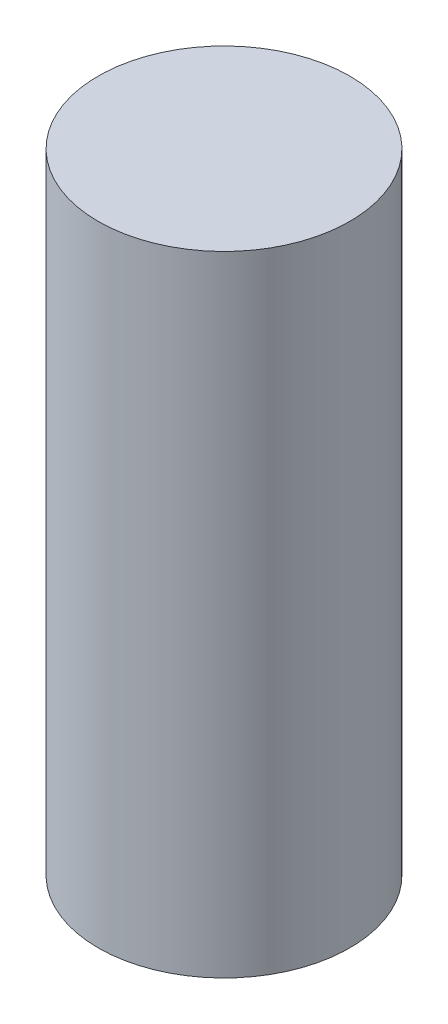
SolidWorks part; units mm, degrees
ref_plane "Front Plane" through (0, 0, 0) normal (0, 0, 1) x (1, 0, 0)
ref_plane "Top Plane" through (0, 0, 0) normal (0, 1, 0) x (1, 0, 0)
ref_plane "Right Plane" through (0, 0, 0) normal (1, 0, 0) x (0, 0, -1)
sketch "Sketch1" plane through (0, 0, 0) normal (0, 1, 0) x (1, 0, 0)
  circle A0 centre (0, 0) radius 1
  dimension "D1" = 2
extrude "Boss-Extrude1" add sketch "Sketch1" along normal blind 5
